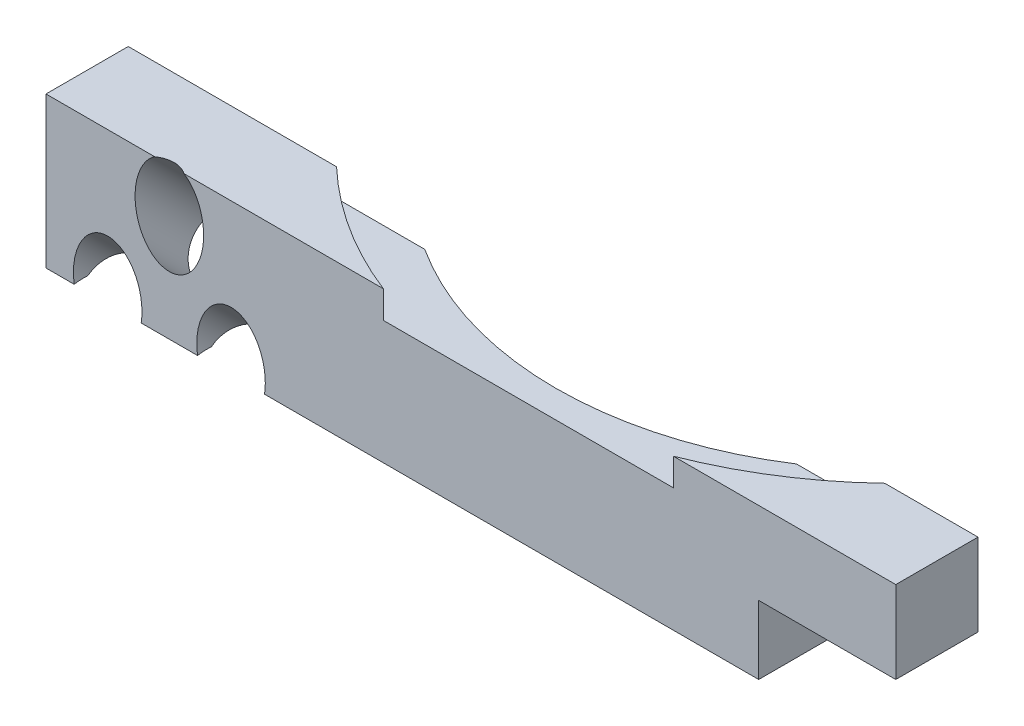
SolidWorks part; units mm, degrees
ref_plane "Спереди" through (0, 0, 0) normal (0, 0, 1) x (1, 0, 0)
ref_plane "Сверху" through (0, 0, 0) normal (0, 1, 0) x (1, 0, 0)
ref_plane "Справа" through (0, 0, 0) normal (1, 0, 0) x (0, 0, -1)
sketch "Эскиз1" plane through (0, 0, 0) normal (0, 0, 1) x (1, 0, 0)
  line L1 (-35.2, -5.5) -> (35.2, -5.5)
  line L2 (-35.2, -5.5) -> (-35.2, 5.5)
  line L3 (-35.2, 5.5) -> (35.2, 5.5)
  line L4 (35.2, -5.5) -> (35.2, 5.5)
  line L5 (-35.2, -5.5) -> (35.2, 5.5) construction
  line L6 (-35.2, 5.5) -> (35.2, -5.5) construction
  point P0 (0, 0)
  dimension "D1" = 70.4
  dimension "D2" = 11
extrude "Бобышка-Вытянуть1" add sketch "Эскиз1" along normal blind 6
sketch "Эскиз3" plane through (0, 5.5, 0) normal (0, 1, 0) x (1, 0, 0)
  line L0 (35.2, 0) -> (-35.2, 0) construction
  line L1 (35.2, -6) -> (-35.2, -6) construction
  arc A0 (-13.5647, 0) -> (13.5647, 0) centre (0, 21) ccw
  line M1 (35.2, 0) -> (-35.2, 0)
  dimension "D1" = 25
  dimension "D2" = 27
extrude "Вырез-Вытянуть1" cut sketch "Эскиз3" against normal blind 6.5 contours A0 M1
sketch "Эскиз4" plane through (0, 5.5, 0) normal (0, 1, 0) x (1, 0, 0)
  line L0 (35.2, -6) -> (-35.2, -6) construction
  arc A0 (3.873, -6) -> (-3.873, -6) centre (0, -13) ccw
  dimension "D1" = 8
  dimension "D2" = 7
extrude "Вырез-Вытянуть2" [suppressed] cut sketch "Эскиз4" against normal through all and the other way through all
sketch "Эскиз6" plane through (-35.2, 0, 0) normal (-1, 0, 0) x (0, 0, 1)
  line L0 (0, -0.5503) -> (4.9497, -5.5)
  line L1 (0, 5.5) -> (0, -5.5) construction
  line L2 (6, -5.5) -> (0, -5.5) construction
  line M1 (0, 5.5) -> (0, -5.5)
  line M2 (0, -5.5) -> (6, -5.5)
  dimension "D1" = 45
  dimension "D2" = 3.5
extrude "Вырез-Вытянуть3" cut sketch "Эскиз6" against normal blind 17 contours L0 M1 M2
sketch "Эскиз7" plane through (0, 5.5, 0) normal (0, 1, 0) x (1, 0, 0)
  line L0 (-13.5647, 0) -> (-35.2, 0) construction
  line L1 (35.2, 0) -> (13.5647, 0) construction
  arc A0 (-20, 0) -> (20, 0) centre (0, 21) ccw
  arc A1 (-13.5647, 0) -> (13.5647, 0) centre (0, 21) ccw construction
  line M1 (35.2, 0) -> (13.5647, 0)
  arc M2 (13.5647, 0) -> (-13.5647, 0) centre (0, 21) cw
  line M3 (-13.5647, 0) -> (-35.2, 0)
  line M5 (-35.2, -6) -> (35.2, -6)
  dimension "D1" = 29
extrude "Вырез-Вытянуть4" cut sketch "Эскиз7" against normal blind 2 contours A0 M5 M1 M2 M3
sketch "Эскиз9" plane through (0, 5.5, 0) normal (0, 1, 0) x (1, 0, 0)
  line L0 (26.8, 0) -> (26.8, -6)
  line L1 (35.2, 0) -> (20, 0) construction
  line L2 (35.2, -6) -> (10.583, -6) construction
  line L3 (-35.2, -6) -> (-35.2, 0) construction
  dimension "D1" = 62
extrude "Вырез-Вытянуть5" cut sketch "Эскиз9" against normal through all
sketch "Эскиз10" plane through (0, 0, 6) normal (0, 0, 1) x (1, 0, 0)
  line L0 (16.8, -5.5) -> (16.8, -0.5)
  line L1 (-35.2, -5.5) -> (26.8, -5.5) construction
  line L2 (16.8, -0.5) -> (26.8, -0.5)
  line L3 (26.8, 5.5) -> (26.8, -5.5) construction
  line L4 (26.8, 5.5) -> (10.583, 5.5) construction
  line L5 (-35.2, 5.5) -> (-35.2, -5.5) construction
  dimension "D1" = 52
  dimension "D2" = 6
extrude "Вырез-Вытянуть6" cut sketch "Эскиз10" against normal through all flip side to cut
sketch "Эскиз11" plane through (0, -0.2751, -0.2751) normal (0, -0.7071, -0.7071) x (1, 0, 0)
  line L0 (-20, -3.8891) -> (-35.2, -3.8891) construction
  line L1 (-35.2, -3.8891) -> (-35.2, 0.3891) construction
  circle A0 centre (-26.2, 2.6109) radius 2.5
  circle A1 centre (-30.7, 7.6109) radius 2.5
  circle A2 centre (-21.7, 7.6109) radius 2.5
  dimension "D3" = 4.5
  dimension "D4" = 4.5
  dimension "D5" = 5
  dimension "D6" = 5
  dimension "D7" = 5
  dimension "D1" = 6.5
  dimension "D2" = 9
extrude "Вырез-Вытянуть7" cut sketch "Эскиз11" against normal through all
